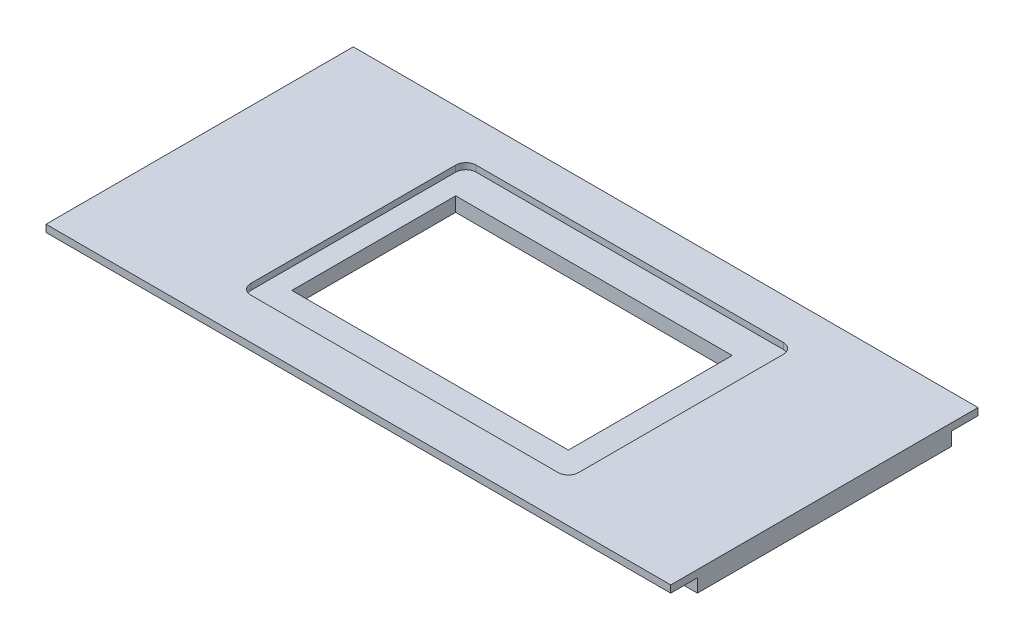
SolidWorks part; units mm, degrees
ref_plane "Front Plane" through (0, 0, 0) normal (0, 0, 1) x (1, 0, 0)
ref_plane "Top Plane" through (0, 0, 0) normal (0, 1, 0) x (1, 0, 0)
ref_plane "Right Plane" through (0, 0, 0) normal (1, 0, 0) x (0, 0, -1)
sketch "Sketch2" plane through (0, 0, 0) normal (0, 1, 0) x (1, 0, 0)
  line L1 (-152.5, 75) -> (152.5, 75)
  line L2 (-152.5, 75) -> (-152.5, -75)
  line L3 (-152.5, -75) -> (152.5, -75)
  line L4 (152.5, 75) -> (152.5, -75)
  line L5 (-152.5, 75) -> (152.5, -75) construction
  line L6 (-152.5, -75) -> (152.5, 75) construction
  point P0 (0, 0)
  dimension "D1" = 305
  dimension "D2" = 150
extrude "Boss-Extrude1" add sketch "Sketch2" along normal mid plane 10
sketch "Sketch3" plane through (152.5, 0, 0) normal (1, 0, 0) x (0, 0, -1)
  line L0 (-75, 5) -> (75, 5) construction
  line L1 (-75, -5) -> (-62, -5)
  line L2 (-75, -5) -> (-75, 1.5)
  line L3 (-75, 1.5) -> (-62, 1.5)
  line L4 (-62, -5) -> (-62, 1.5)
  line L5 (75, -5) -> (62, -5)
  line L6 (75, -5) -> (75, 1.5)
  line L7 (75, 1.5) -> (62, 1.5)
  line L8 (62, -5) -> (62, 1.5)
  dimension "D1" = 3.5
  dimension "D2" = 13
extrude "Cut-Extrude1" cut sketch "Sketch3" against normal up to surface (305 mm away) up to face at (-152.5, 0, 0)
sketch "Sketch4" plane through (0, 5, 0) normal (0, 1, 0) x (1, 0, 0)
  line L0 (-152.5, -75) -> (152.5, -75) construction
  line L1 (-77.5, -55) -> (82.5, -55)
  line L2 (-77.5, -55) -> (-77.5, 55)
  line L3 (-77.5, 55) -> (82.5, 55)
  line L4 (82.5, -55) -> (82.5, 55)
  line L5 (-152.5, 75) -> (-152.5, -75) construction
  dimension "D1" = 20
  dimension "D2" = 75
  dimension "D3" = 160
  dimension "D4" = 110
extrude "Cut-Extrude2" cut sketch "Sketch4" against normal blind 3
fillet "Fillet1" radius 5 4 edges at (-77.5, 3.5, 55) (82.5, 3.5, 55) (82.5, 3.5, -55) (-77.5, 3.5, -55)
sketch "Sketch5" plane through (0, 2, 0) normal (0, 1, 0) x (1, 0, 0)
  line L0 (82.5, -50) -> (82.5, 50) construction
  line L1 (-67.5, 40) -> (67.5, 40)
  line L2 (-67.5, 40) -> (-67.5, -40)
  line L3 (-67.5, -40) -> (67.5, -40)
  line L4 (67.5, 40) -> (67.5, -40)
  line L5 (-67.5, 40) -> (67.5, -40) construction
  line L6 (-67.5, -40) -> (67.5, 40) construction
  line L7 (77.5, 55) -> (-72.5, 55) construction
  point P0 (0, 0)
  dimension "D1" = 15
  dimension "D2" = 15
extrude "Cut-Extrude3" cut sketch "Sketch5" against normal through all
equation "\"∩╗┐cas_w\" = 38.1mm"
equation "\"cas_l\" = 83.0mm"
equation "\"cas_h\" = 280.0mm"
equation "\"rail_w\" = 50.5mm"
equation "\"rail_c\" = 10.5mm"
equation "\"stinset_l\" = 160mm"
equation "\"stinset_w\" = 110mm"
equation "\"stinset_h\" = 3mm"
equation "\"stinset_fillet\" = 5mm"
equation "\"slide_l\" = 75.6mm"
equation "\"slide_w\" = 26mm"
equation "\"slide_h\" = 1.07mm"
equation "\"slide_fillet\" = 1mm"
equation "\"stxslide_l\" = 305mm"
equation "\"stxslide_w\" = 150mm"
equation "\"stxslide_h\" = 10mm"
equation "\"D1@Sketch2\"=\"stxslide_l\""
equation "\"D2@Sketch2\"=\"stxslide_w\""
equation "\"D1@Boss-Extrude1\"=\"stxslide_h\""
equation "\"D3@Sketch4\"=\"stinset_l\""
equation "\"D4@Sketch4\"=\"stinset_w\""
equation "\"D1@Cut-Extrude2\"=\"stinset_h\""
equation "\"D1@Fillet1\"=\"stinset_fillet\""
